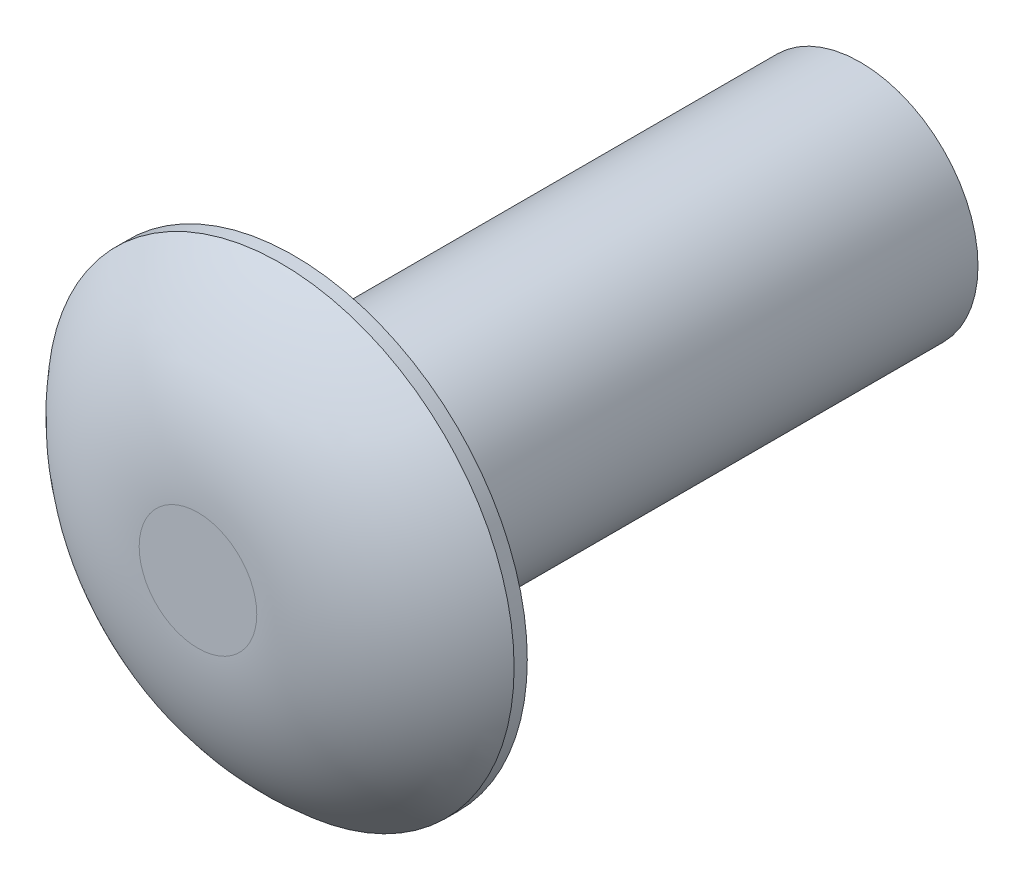
SolidWorks part; units mm, degrees
ref_plane "Front" through (0, 0, 0) normal (0, 0, 1) x (1, 0, 0)
ref_plane "Top" through (0, 0, 0) normal (0, 1, 0) x (1, 0, 0)
ref_plane "Right" through (0, 0, 0) normal (1, 0, 0) x (0, 0, -1)
sketch "layout" plane through (0, 0, 0) normal (1, 0, 0) x (0, 0, -1)
  line L0 (-16.5862, 0) -> (-1.2954, 0) construction
  line L1 (-1.2954, 0) -> (0, 0) construction
  line L2 (0, 0) -> (7.6454, 0) construction
  line L3 (7.6454, 0) -> (8.9408, 0) construction
  line L8 (0, 3.1496) -> (0, -3.1496) construction
  line L9 (7.6454, 1.5875) -> (7.6454, -1.5875) construction
  point P7 (-1.2954, 3.1496)
  point P10 (0, 3.1496)
  point P17 (0, -3.1496)
  point P18 (7.6454, 1.5875)
  point P19 (-16.5862, 0)
  point P21 (7.6454, -1.5875)
  dimension "D5" = 1.2954
sketch "Sketch2" plane through (0, 0, 0) normal (1, 0, 0) x (0, 0, -1)
  line L0 (-16.5862, 0) -> (-16.5862, 0.7937)
  line L1 (-16.5862, 0.7937) -> (0, 0.7937) construction
  line L2 (0, 3.1496) -> (0, -3.1496) construction
  line L3 (0, 0) -> (0, 3.1496) construction
  line L4 (-1.2954, 0) -> (-1.2954, -1.8472) construction
  line L5 (7.6454, 1.5875) -> (0, 1.5875)
  line L6 (7.6454, 1.5875) -> (7.6454, 0) construction
  line L7 (7.9692, 1.5875) -> (7.9692, -1.5875) construction
  line L8 (6.9977, 0) -> (7.6454, 0) construction
  line L9 (8.9408, 0) -> (8.9408, 1.5875) construction
  line L10 (7.6454, 1.5875) -> (7.9692, 1.5875) construction
  line L11 (7.9692, 1.5875) -> (8.2931, 1.5875) construction
  line L12 (-16.5862, 0) -> (7.6454, 0)
  line L13 (-1.2954, 0.7938) -> (-1.2954, 0) construction
  line L14 (8.2931, 1.5875) -> (8.6169, 1.5875) construction
  line L15 (8.6169, 1.5875) -> (8.9408, 1.5875) construction
  line L16 (7.6454, 1.4967) -> (7.6454, 1.5875)
  line L17 (7.6454, 1.4967) -> (7.6454, 0)
  line L19 (0, 1.5875) -> (0, 3.1496)
  line L20 (-1.2954, 0.7938) -> (-16.5862, 0.7937)
  line L22 (0, 3.1496) -> (-0.1778, 3.1496)
  arc A2 (-0.1778, 3.1496) -> (-1.2954, 0.7938) centre (1.7464, 0.7938) ccw
  ellipse E0 centre (7.9692, 0) end of major axis (7.9692, -1.5875) minor radius 0.9715 (8.9408, 0) -> (7.6454, 1.4967) ccw construction
  point P20 (7.6454, 0.7937)
  dimension "D1" = 0.1778
revolve "Revolve1" add sketch "Sketch2" angle 360 about L12
sketch "Sketch3" plane through (0, 0, 0) normal (0, 1, 0) x (1, 0, 0)
  line L0 (0, -16.5862) -> (0.997, -15.2869)
  line L1 (-0.7937, -16.5862) -> (0.7937, -16.5862) construction
  line L3 (0, -16.5862) -> (0, -17.0942) construction
  line L4 (0, -16.5862) -> (-0.997, -15.2869)
  line L5 (-0.997, -15.2869) -> (-0.9969, -17.0942)
  line L6 (-0.9969, -17.0942) -> (0.997, -17.0942)
  line L7 (0.997, -17.0942) -> (0.997, -15.2869)
  dimension "D1" = 75
  dimension "D2" = 0.2032
  dimension "D3" = 0.508
extrude "Cut-Extrude1" cut sketch "Sketch3" against normal through all both and the other way through all
sketch "Sketch5" plane through (0, 0, 0) normal (1, 0, 0) x (0, 0, -1)
  line L0 (-16.5862, 0) -> (-15.5518, 1.1112)
  line L1 (-16.5862, -0.7937) -> (-16.5862, 0.7938) construction
  line L2 (-15.5518, 1.1112) -> (-16.9037, 1.1112)
  line L3 (-16.9037, 1.1112) -> (-16.9037, -1.1112)
  line L4 (-16.9037, -1.1112) -> (-15.5518, -1.1112)
  line L5 (-15.5518, -1.1112) -> (-16.5862, 0)
  line L6 (-16.5862, 0) -> (-9.2614, 0) construction
  line L7 (-1.2954, 0.7938) -> (-16.5862, 0.7938) construction
  line L8 (-15.5518, 0) -> (-15.5518, 1.1112) construction
  ellipse E0 centre (-16.5862, 0) end of major axis (-17.6206, 0) minor radius 0.7937 (-16.5862, -0.7937) -> (-16.5862, 0.7937) ccw construction
  dimension "D1" = 0.3175
  dimension "D2" = 0.3175
extrude "Cut-Extrude2" cut sketch "Sketch5" against normal through all both and the other way through all
fillet "Fillet2" radius 0.254 1 edges at (1.5875, 0, 0)
sketch "Sketch6" plane through (0, 0, 0) normal (1, 0, 0) x (0, 0, -1)
  line L0 (-5.2705, 0.7938) -> (-5.1181, 0.7938)
  line L1 (-16.5862, 0) -> (-1.2954, 0) construction
  line L2 (-5.1181, 0.7938) -> (-5.1181, -0.7938) construction
  line L3 (-1.2954, 0.7938) -> (-1.2954, -0.7938) construction
  line L4 (-15.8473, -0.7938) -> (-1.2954, -0.7938) construction
  arc A0 (-5.2705, 0.7938) -> (-5.1181, 0.7938) centre (-5.1943, 0.7938) ccw
  point P11 (-5.1181, 0)
  dimension "D2" = 0.0762
  dimension "D1" = 11.4681
  dimension "D3" = 15.2908
revolve "Cut-Revolve1" [suppressed] cut sketch "Sketch6" angle 360 about L1
pattern_linear "LPattern1" [suppressed] count 18 spacing 0.762 along (0, 0, -1)
sketch "Sketch7" plane through (0, 0, 0) normal (0, 1, 0) x (1, 0, 0)
  line L0 (0.7938, -1.2954) -> (-0.7938, -1.2954) construction
  line L1 (-0.7938, -1.2954) -> (1.0472, -1.2954)
  line L2 (-0.7938, -1.2954) -> (-0.7938, -17.4311)
  line L3 (-0.7938, -17.4311) -> (1.0472, -17.4311)
  line L4 (1.0472, -1.2954) -> (1.0472, -17.4311)
  line L5 (-0.7938, -1.2954) -> (-0.7938, -15.5518) construction
extrude "Cut-Extrude3" cut sketch "Sketch7" against normal through all and the other way through all
equation "\"D5@layout\"=\"Head Height@layout\"*1"
equation "\"D9@layout\"=\"length@layout\"*2"
equation "\"D2@Sketch5\"=\"D1@Sketch5\""
equation "\"D1@Sketch6\"=\"D3@Sketch6\"*.75"
